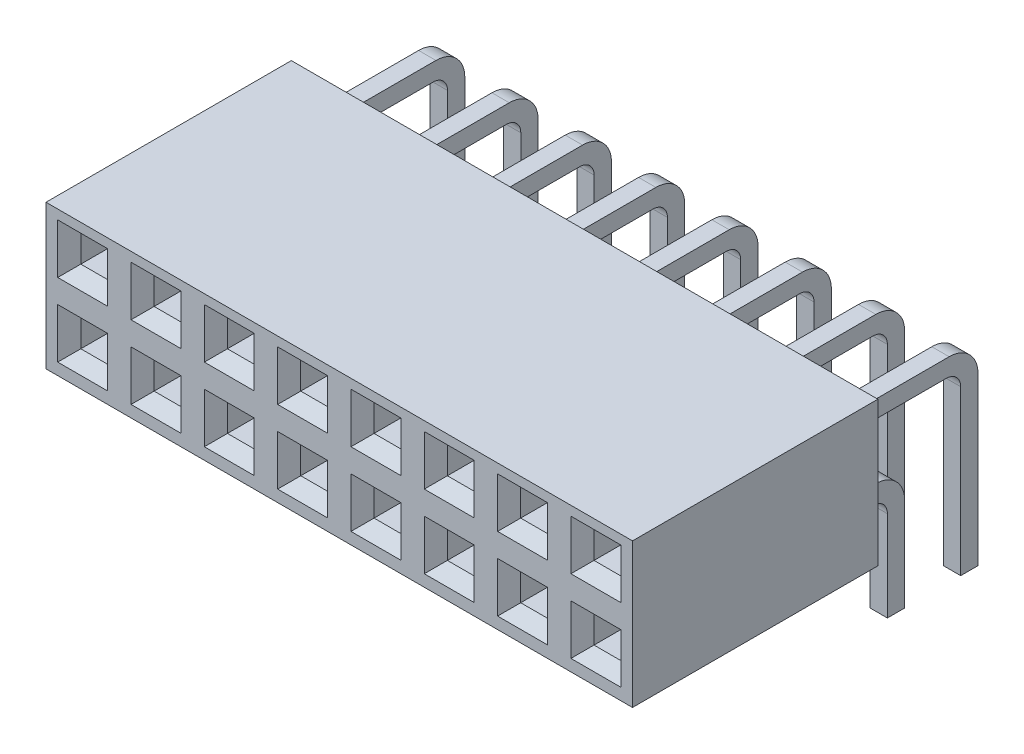
SolidWorks part; units mm, degrees
ref_plane "Спереди" through (0, 0, 0) normal (0, 0, 1) x (1, 0, 0)
ref_plane "Сверху" through (0, 0, 0) normal (0, 1, 0) x (1, 0, 0)
ref_plane "Справа" through (0, 0, 0) normal (1, 0, 0) x (0, 0, -1)
sketch "Эскиз1" plane through (0, 0, 0) normal (0, 0, 1) x (1, 0, 0)
  line L1 (-10.16, 2.5) -> (10.16, 2.5)
  line L2 (-10.16, 2.5) -> (-10.16, -2.5)
  line L3 (-10.16, -2.5) -> (10.16, -2.5)
  line L4 (10.16, 2.5) -> (10.16, -2.5)
  line L5 (-10.16, 2.5) -> (10.16, -2.5) construction
  line L6 (-10.16, -2.5) -> (10.16, 2.5) construction
  point P0 (0, 0)
  point P6 (0, 2.5)
  dimension "D1" = 5
  dimension "D2" = 20.32
extrude "Бобышка-Вытянуть1" add sketch "Эскиз1" against normal blind 8.5
sketch "Эскиз2" plane through (0, 0, 0) normal (0, 0, 1) x (1, 0, 0)
  line L0 (-10.16, -2.5) -> (10.16, -2.5) construction
  line L1 (-9.3541, -0.7659) -> (-8.4259, -0.7659)
  line L2 (-9.3541, -0.7659) -> (-9.3541, -1.6941)
  line L3 (-9.3541, -1.6941) -> (-8.4259, -1.6941)
  line L4 (-8.4259, -0.7659) -> (-8.4259, -1.6941)
  line L5 (-9.3541, -0.7659) -> (-8.4259, -1.6941) construction
  line L6 (-9.3541, -1.6941) -> (-8.4259, -0.7659) construction
  line L11 (-10.16, 2.5) -> (-10.16, -2.5) construction
  line L12 (-6.8141, -0.7659) -> (-6.8141, -1.6941)
  line L13 (-6.8141, -0.7659) -> (-5.8859, -0.7659)
  line L14 (-5.8859, -0.7659) -> (-5.8859, -1.6941)
  line L15 (-6.8141, -1.6941) -> (-5.8859, -1.6941)
  line L16 (-4.2741, -0.7659) -> (-4.2741, -1.6941)
  line L17 (-4.2741, -0.7659) -> (-3.3459, -0.7659)
  line L18 (-3.3459, -0.7659) -> (-3.3459, -1.6941)
  line L19 (-4.2741, -1.6941) -> (-3.3459, -1.6941)
  line L20 (-1.7341, -0.7659) -> (-1.7341, -1.6941)
  line L21 (-1.7341, -0.7659) -> (-0.8059, -0.7659)
  line L22 (-0.8059, -0.7659) -> (-0.8059, -1.6941)
  line L23 (-1.7341, -1.6941) -> (-0.8059, -1.6941)
  line L24 (0.8059, -0.7659) -> (0.8059, -1.6941)
  line L25 (0.8059, -0.7659) -> (1.7341, -0.7659)
  line L26 (1.7341, -0.7659) -> (1.7341, -1.6941)
  line L27 (0.8059, -1.6941) -> (1.7341, -1.6941)
  line L28 (3.3459, -0.7659) -> (3.3459, -1.6941)
  line L29 (3.3459, -0.7659) -> (4.2741, -0.7659)
  line L30 (4.2741, -0.7659) -> (4.2741, -1.6941)
  line L31 (3.3459, -1.6941) -> (4.2741, -1.6941)
  line L32 (5.8859, -0.7659) -> (5.8859, -1.6941)
  line L33 (5.8859, -0.7659) -> (6.8141, -0.7659)
  line L34 (6.8141, -0.7659) -> (6.8141, -1.6941)
  line L35 (5.8859, -1.6941) -> (6.8141, -1.6941)
  line L36 (8.4259, -0.7659) -> (8.4259, -1.6941)
  line L37 (8.4259, -0.7659) -> (9.3541, -0.7659)
  line L38 (9.3541, -0.7659) -> (9.3541, -1.6941)
  line L39 (8.4259, -1.6941) -> (9.3541, -1.6941)
  line L40 (-6.8141, 1.7741) -> (-6.8141, 0.8459)
  line L41 (-6.8141, 1.7741) -> (-5.8859, 1.7741)
  line L42 (-5.8859, 1.7741) -> (-5.8859, 0.8459)
  line L43 (-6.8141, 0.8459) -> (-5.8859, 0.8459)
  line L44 (-4.2741, 1.7741) -> (-4.2741, 0.8459)
  line L45 (-4.2741, 1.7741) -> (-3.3459, 1.7741)
  line L46 (-3.3459, 1.7741) -> (-3.3459, 0.8459)
  line L47 (-4.2741, 0.8459) -> (-3.3459, 0.8459)
  line L48 (-1.7341, 1.7741) -> (-1.7341, 0.8459)
  line L49 (-1.7341, 1.7741) -> (-0.8059, 1.7741)
  line L50 (-0.8059, 1.7741) -> (-0.8059, 0.8459)
  line L51 (-1.7341, 0.8459) -> (-0.8059, 0.8459)
  line L52 (0.8059, 1.7741) -> (0.8059, 0.8459)
  line L53 (0.8059, 1.7741) -> (1.7341, 1.7741)
  line L54 (1.7341, 1.7741) -> (1.7341, 0.8459)
  line L55 (0.8059, 0.8459) -> (1.7341, 0.8459)
  line L56 (3.3459, 1.7741) -> (3.3459, 0.8459)
  line L57 (3.3459, 1.7741) -> (4.2741, 1.7741)
  line L58 (4.2741, 1.7741) -> (4.2741, 0.8459)
  line L59 (3.3459, 0.8459) -> (4.2741, 0.8459)
  line L60 (5.8859, 1.7741) -> (5.8859, 0.8459)
  line L61 (5.8859, 1.7741) -> (6.8141, 1.7741)
  line L62 (6.8141, 1.7741) -> (6.8141, 0.8459)
  line L63 (5.8859, 0.8459) -> (6.8141, 0.8459)
  line L64 (8.4259, 1.7741) -> (8.4259, 0.8459)
  line L65 (8.4259, 1.7741) -> (9.3541, 1.7741)
  line L66 (9.3541, 1.7741) -> (9.3541, 0.8459)
  line L67 (8.4259, 0.8459) -> (9.3541, 0.8459)
  line L68 (-9.3541, 1.7741) -> (-9.3541, 0.8459)
  line L69 (-9.3541, 1.7741) -> (-8.4259, 1.7741)
  line L70 (-8.4259, 1.7741) -> (-8.4259, 0.8459)
  line L71 (-9.3541, 0.8459) -> (-8.4259, 0.8459)
  point P0 (-8.89, -1.23)
  dimension "D1" = 1.27
  dimension "D2" = 1.27
  dimension "D3" = 8
  dimension "D4" = 2
extrude "Вырез-Вытянуть1" cut sketch "Эскиз2" against normal blind 6
chamfer "Фаска1" distance 0.4 angle 45 64 edges at (-8.89, -1.6941, 0) (-8.4259, -1.23, 0) (-8.89, -0.7659, 0) (-9.3541, -1.23, 0) (-6.8141, -1.23, 0) (-6.35, -1.6941, 0) (-5.8859, -1.23, 0) (-6.35, -0.7659, 0) (-3.81, -1.6941, 0) (-3.3459, -1.23, 0) (-3.81, -0.7659, 0) (-4.2741, -1.23, 0) (-1.27, -1.6941, 0) (-0.8059, -1.23, 0) (-1.27, -0.7659, 0) (-1.7341, -1.23, 0) (1.27, -1.6941, 0) (1.7341, -1.23, 0) (1.27, -0.7659, 0) (0.8059, -1.23, 0) (3.81, -1.6941, 0) (4.2741, -1.23, 0) (3.81, -0.7659, 0) (3.3459, -1.23, 0) (6.35, -1.6941, 0) (6.8141, -1.23, 0) (6.35, -0.7659, 0) (5.8859, -1.23, 0) (9.3541, -1.23, 0) (8.89, -0.7659, 0) (8.4259, -1.23, 0) (8.89, -1.6941, 0) (8.89, 0.8459, 0) (9.3541, 1.31, 0) (8.89, 1.7741, 0) (8.4259, 1.31, 0) (6.35, 0.8459, 0) (6.8141, 1.31, 0) (6.35, 1.7741, 0) (5.8859, 1.31, 0) (3.3459, 1.31, 0) (3.81, 1.7741, 0) (4.2741, 1.31, 0) (3.81, 0.8459, 0) (1.27, 0.8459, 0) (0.8059, 1.31, 0) (1.27, 1.7741, 0) (1.7341, 1.31, 0) (-0.8059, 1.31, 0) (-1.27, 1.7741, 0) (-1.7341, 1.31, 0) (-1.27, 0.8459, 0) (-3.81, 0.8459, 0) (-3.3459, 1.31, 0) (-3.81, 1.7741, 0) (-4.2741, 1.31, 0) (-6.35, 0.8459, 0) (-5.8859, 1.31, 0) (-6.35, 1.7741, 0) (-6.8141, 1.31, 0) (-8.89, 0.8459, 0) (-9.3541, 1.31, 0) (-8.89, 1.7741, 0) (-8.4259, 1.31, 0)
ref_plane "Плоскость4" through (-8.89, 0, 0) normal (-1, 0, 0) x (0, 0, 1)
sketch "Эскиз3" plane through (-8.89, 0, 0) normal (-1, 0, 0) x (0, 0, 1)
  line L0 (-8.5, 1.57) -> (-11.94, 1.57)
  line L1 (-8.5, 2.5) -> (-8.5, -2.5) construction
  line L2 (-12.94, 0.57) -> (-12.94, -5.4)
  line L3 (-12.94, -5.4) -> (-12.34, -5.4)
  line L4 (-12.34, -5.4) -> (-12.34, 0.47)
  line L5 (-11.84, 0.97) -> (-8.5, 0.97)
  line L6 (-8.5, 0.97) -> (-8.5, 1.57)
  line L7 (-8.5, -0.97) -> (-9.4, -0.97)
  line L8 (-10.4, -1.97) -> (-10.4, -5.4)
  line L9 (-10.4, -5.4) -> (-9.8, -5.4)
  line L10 (-9.8, -5.4) -> (-9.8, -2.07)
  line L11 (-9.3, -1.57) -> (-8.5, -1.57)
  line L12 (-8.5, -1.57) -> (-8.5, -0.97)
  line L13 (-8.5, 1.27) -> (-8.5, -1.27) construction
  line L14 (0, 0) -> (-8.5, 0) construction
  line L15 (0, 2.5) -> (0, -2.5) construction
  line L16 (-8.5, -2.5) -> (0, -2.5) construction
  arc A0 (-9.4, -0.97) -> (-10.4, -1.97) centre (-9.4, -1.97) ccw
  arc A1 (-11.94, 1.57) -> (-12.94, 0.57) centre (-11.94, 0.57) ccw
  arc A2 (-9.8, -2.07) -> (-9.3, -1.57) centre (-9.3, -2.07) cw
  arc A3 (-12.34, 0.47) -> (-11.84, 0.97) centre (-11.84, 0.47) cw
  point P16 (-12.64, -5.4)
  point P17 (-10.1, -5.4)
  dimension "D6" = 1
  dimension "D7" = 0.5
  dimension "D1" = 2.54
  dimension "D2" = 1.6
  dimension "D3" = 0.6
  dimension "D4" = 2.54
  dimension "D5" = 2.9
extrude "Бобышка-Вытянуть2" add sketch "Эскиз3" along normal mid plane 0.6
pattern_linear "Линейный массив1" count 8 spacing 2.54 along (1, 0, 0) of "Бобышка-Вытянуть2"
chamfer "Фаска2" distance 0.2 angle 45 64 edges at (8.89, -5.4, -10.4) (8.59, -5.4, -10.1) (8.89, -5.4, -9.8) (9.19, -5.4, -10.1) (8.89, -5.4, -12.94) (8.59, -5.4, -12.64) (8.89, -5.4, -12.34) (9.19, -5.4, -12.64) (6.35, -5.4, -10.4) (6.05, -5.4, -10.1) (6.35, -5.4, -9.8) (6.65, -5.4, -10.1) (6.35, -5.4, -12.94) (6.05, -5.4, -12.64) (6.35, -5.4, -12.34) (6.65, -5.4, -12.64) (3.81, -5.4, -10.4) (3.51, -5.4, -10.1) (3.81, -5.4, -9.8) (4.11, -5.4, -10.1) (3.81, -5.4, -12.94) (3.51, -5.4, -12.64) (3.81, -5.4, -12.34) (4.11, -5.4, -12.64) (1.27, -5.4, -10.4) (0.97, -5.4, -10.1) (1.27, -5.4, -9.8) (1.57, -5.4, -10.1) (1.27, -5.4, -12.94) (0.97, -5.4, -12.64) (1.27, -5.4, -12.34) (1.57, -5.4, -12.64) (-1.27, -5.4, -10.4) (-1.57, -5.4, -10.1) (-1.27, -5.4, -9.8) (-0.97, -5.4, -10.1) (-1.27, -5.4, -12.94) (-1.57, -5.4, -12.64) (-1.27, -5.4, -12.34) (-0.97, -5.4, -12.64) (-3.81, -5.4, -10.4) (-4.11, -5.4, -10.1) (-3.81, -5.4, -9.8) (-3.51, -5.4, -10.1) (-3.81, -5.4, -12.94) (-4.11, -5.4, -12.64) (-3.81, -5.4, -12.34) (-3.51, -5.4, -12.64) (-6.35, -5.4, -12.94) (-6.65, -5.4, -12.64) (-6.35, -5.4, -12.34) (-6.05, -5.4, -12.64) (-6.35, -5.4, -10.4) (-6.65, -5.4, -10.1) (-6.35, -5.4, -9.8) (-6.05, -5.4, -10.1) (-8.89, -5.4, -10.4) (-9.19, -5.4, -10.1) (-8.89, -5.4, -9.8) (-8.59, -5.4, -10.1) (-8.89, -5.4, -12.94) (-9.19, -5.4, -12.64) (-8.89, -5.4, -12.34) (-8.59, -5.4, -12.64)
